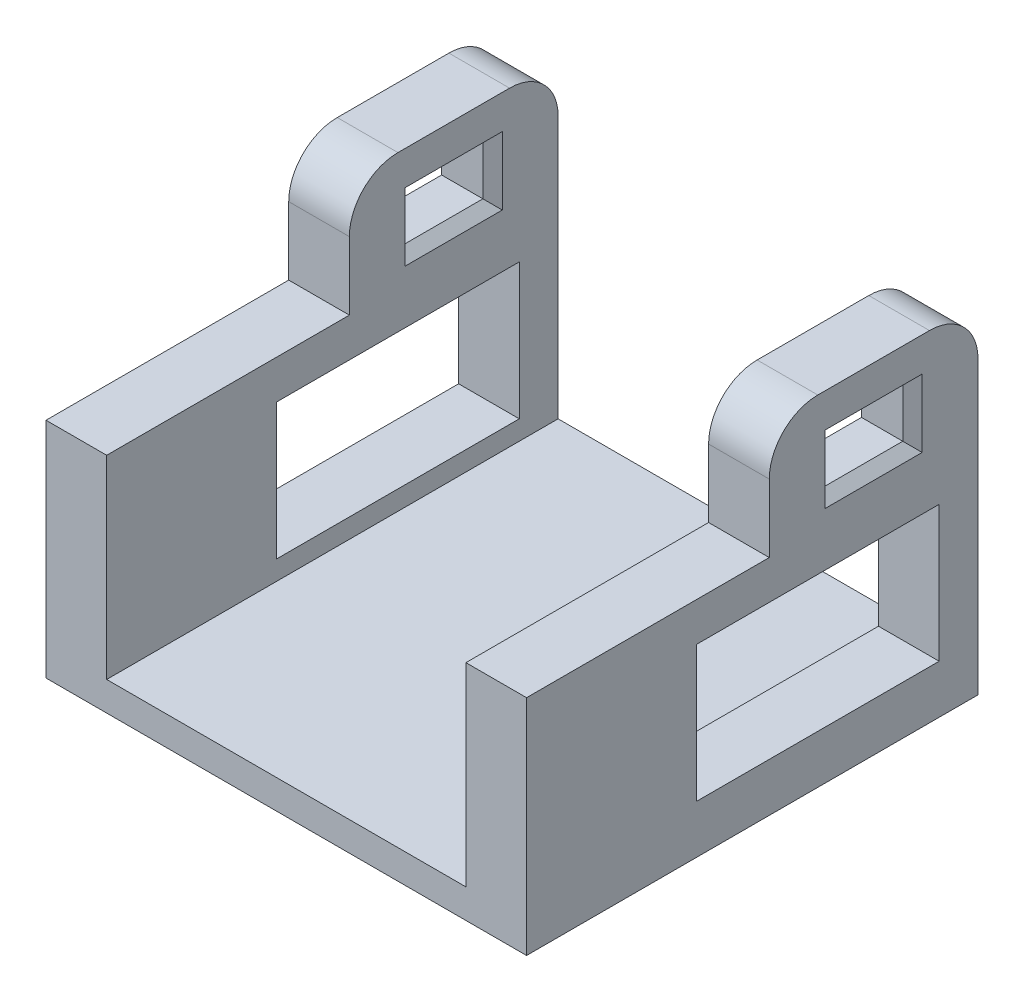
SolidWorks part; units mm, degrees
ref_plane "前视基准面" through (0, 0, 0) normal (0, 0, 1) x (1, 0, 0)
ref_plane "上视基准面" through (0, 0, 0) normal (0, 1, 0) x (1, 0, 0)
ref_plane "右视基准面" through (0, 0, 0) normal (1, 0, 0) x (0, 0, -1)
sketch "草图1" plane through (0, 0, 0) normal (0, 1, 0) x (1, 0, 0)
  line L1 (-24.75, -10.75) -> (24.75, -10.75)
  line L2 (-24.75, -10.75) -> (-24.75, 10.75)
  line L3 (-24.75, 10.75) -> (24.75, 10.75)
  line L4 (24.75, -10.75) -> (24.75, 10.75)
  line L5 (-24.75, -10.75) -> (24.75, 10.75) construction
  line L6 (-24.75, 10.75) -> (24.75, -10.75) construction
  point P0 (0, 0)
  dimension "D1" = 49.5
  dimension "D2" = 21.5
extrude "凸台-拉伸1" add sketch "草图1" along normal blind 3
sketch "草图4" plane through (0, 3, 0) normal (0, 1, 0) x (1, 0, 0)
  line L0 (-24.75, -10.75) -> (24.75, -10.75) construction
  line L1 (-24.75, 10.75) -> (-18.5, 10.75)
  line L2 (-24.75, 10.75) -> (-24.75, -10.75)
  line L3 (-24.75, -10.75) -> (-18.5, -10.75)
  line L4 (-18.5, 10.75) -> (-18.5, -10.75)
  line L5 (0, 0) -> (0, 16.4149) construction
  line L6 (24.75, -10.75) -> (18.5, -10.75)
  line L7 (18.5, 10.75) -> (18.5, -10.75)
  line L8 (24.75, 10.75) -> (18.5, 10.75)
  line L9 (24.75, 10.75) -> (24.75, -10.75)
  dimension "D1" = 6.25
extrude "凸台-拉伸2" add sketch "草图4" along normal blind 20
sketch "草图6" plane through (0, 0, 10.75) normal (0, 0, 1) x (1, 0, 0)
  line L8 (-24.75, 0) -> (24.75, 0)
  line L9 (24.75, 0) -> (24.75, 23)
  line L10 (24.75, 23) -> (18.5, 23)
  line L11 (18.5, 23) -> (18.5, 3)
  line L12 (18.5, 3) -> (-18.5, 3)
  line L13 (-18.5, 3) -> (-18.5, 23)
  line L14 (-18.5, 23) -> (-24.75, 23)
  line L15 (-24.75, 23) -> (-24.75, 0)
  line L16 (-24.75, 0) -> (24.75, 0)
  line L17 (24.75, 0) -> (24.75, 23)
  line L18 (24.75, 23) -> (18.5, 23)
  line L19 (18.5, 23) -> (18.5, 3)
  line L20 (18.5, 3) -> (-18.5, 3)
  line L21 (-18.5, 3) -> (-18.5, 23)
  line L22 (-18.5, 23) -> (-24.75, 23)
  line L23 (-24.75, 23) -> (-24.75, 0)
  dimension "D1" = 0
extrude "凸台-拉伸3" add sketch "草图6" along normal blind 25
ref_plane "基准面4" through (0, 23, 0) normal (0, 1, 0) x (1, 0, 0)
sketch "草图7" plane through (0, 23, 0) normal (0, 1, 0) x (1, 0, 0)
  line L0 (0, 10.75) -> (0, -40.2578) construction
  line L2 (-18.5, -35.75) -> (-18.5, 10.75) construction
  line L3 (-24.75, 10.75) -> (-18.5, 10.75)
  line L4 (-24.75, 10.75) -> (-24.75, -10.75)
  line L5 (-24.75, -10.75) -> (-18.5, -10.75)
  line L6 (-18.5, 10.75) -> (-18.5, -10.75)
  line L7 (24.75, -10.75) -> (18.5, -10.75)
  line L8 (18.5, 10.75) -> (18.5, -10.75)
  line L9 (24.75, 10.75) -> (18.5, 10.75)
  line L10 (24.75, 10.75) -> (24.75, -10.75)
  dimension "D1" = 21.5
extrude "凸台-拉伸4" add sketch "草图7" along normal blind 12
sketch "草图8" plane through (24.75, 0, 0) normal (1, 0, 0) x (0, 0, -1)
  line L0 (0, 35) -> (0, -3.0697) construction
  line L3 (-4, 25.5) -> (4, 25.5)
  line L4 (-4, 25.5) -> (-4, 30.5)
  line L5 (-4, 30.5) -> (4, 30.5)
  line L6 (4, 25.5) -> (4, 30.5)
  line L7 (25.575, 23) -> (-25.575, 23) construction
  dimension "D1" = 5
  dimension "D2" = 8
  dimension "D3" = 2.5
extrude "切除-拉伸1" cut sketch "草图8" against normal through all
fillet "圆角1" radius 5 2 edges at (-21.625, 35, 10.75) (21.625, 35, 10.75)
fillet "圆角2" radius 5 2 edges at (21.625, 35, -10.75) (-21.625, 35, -10.75)
sketch "草图9" plane through (24.75, 0, 0) normal (1, 0, 0) x (0, 0, -1)
  line L0 (10.75, 30) -> (10.75, 0) construction
  line L1 (-18.25, 19) -> (6.75, 19)
  line L2 (-18.25, 19) -> (-18.25, 5)
  line L3 (-18.25, 5) -> (6.75, 5)
  line L4 (6.75, 19) -> (6.75, 5)
  line L5 (-35.75, 0) -> (10.75, 0) construction
  dimension "D1" = 25
  dimension "D2" = 14
  dimension "D3" = 4
  dimension "D4" = 5
extrude "切除-拉伸2" cut sketch "草图9" against normal through all
chamfer "倒角1" distance 1 angle 45 16 edges at (-24.75, 25.5, 0) (-24.75, 28, 4) (-24.75, 28, -4) (-24.75, 30.5, 0) (18.5, 25.5, 0) (18.5, 28, 4) (18.5, 28, -4) (18.5, 30.5, 0) (-18.5, 28, 4) (-18.5, 25.5, 0) (-18.5, 28, -4) (-18.5, 30.5, 0) (24.75, 28, 4) (24.75, 25.5, 0) (24.75, 28, -4) (24.75, 30.5, 0)
